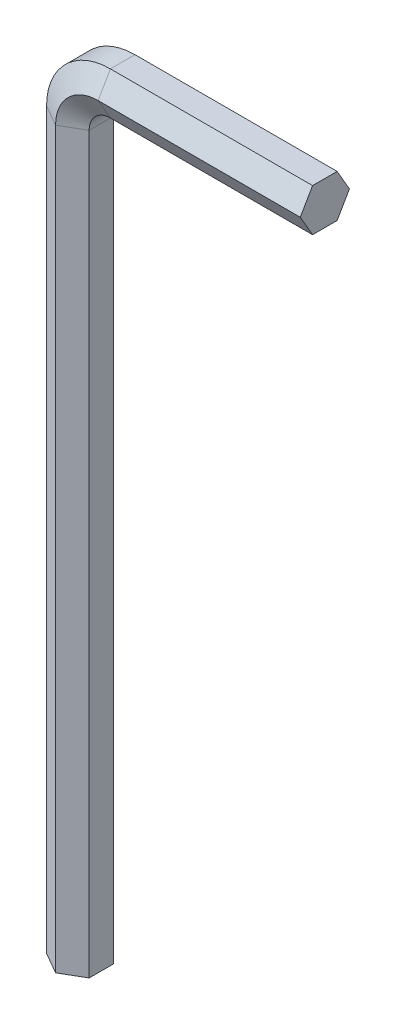
SolidWorks part; units mm, degrees
ref_plane "Front Plane" through (0, 0, 0) normal (0, 0, 1) x (1, 0, 0)
ref_plane "Top Plane" through (0, 0, 0) normal (0, 1, 0) x (1, 0, 0)
ref_plane "Right Plane" through (0, 0, 0) normal (1, 0, 0) x (0, 0, -1)
sketch "Sketch2" plane through (0, 0, 0) normal (0, 0, 1) x (1, 0, 0)
  line L0 (0, 0) -> (0, 69)
  line L1 (6, 75) -> (25, 75)
  arc A0 (0, 69) -> (6, 75) centre (6, 69) cw
  point P6 (15.5, 75)
  dimension "D1" = 6
  dimension "D2" = 75
  dimension "D3" = 25
sketch "Sketch3" plane through (0, 0, 0) normal (0, 1, 0) x (1, 0, 0)
  line L13 (2, 2.3094) -> (0, 1.1547)
  line L14 (0, 1.1547) -> (0, -1.1547)
  line L15 (0, -1.1547) -> (2, -2.3094)
  line L16 (2, -2.3094) -> (4, -1.1547)
  line L17 (4, -1.1547) -> (4, 1.1547)
  line L18 (4, 1.1547) -> (2, 2.3094)
  circle A0 centre (2, 0) radius 2 construction
  dimension "D1" = 4
sweep "Sweep1" add profiles "Sketch3" path "Sketch2"
equation "\"A\"= 1.5mm"
equation "\"B\"= 109mm"
